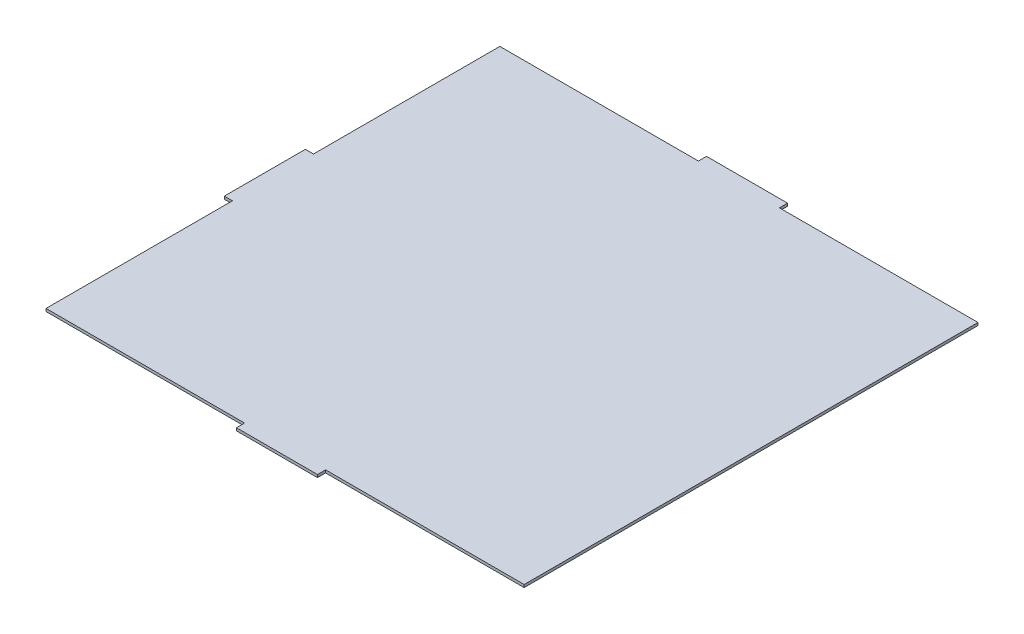
SolidWorks part; units mm, degrees
ref_plane "Front Plane" through (0, 0, 0) normal (0, 0, 1) x (1, 0, 0)
ref_plane "Top Plane" through (0, 0, 0) normal (0, 1, 0) x (1, 0, 0)
ref_plane "Right Plane" through (0, 0, 0) normal (1, 0, 0) x (0, 0, -1)
sketch "Sketch1" plane through (0, 0, 0) normal (0, 1, 0) x (1, 0, 0)
  line L0 (-51.678, 119.992) -> (21.822, 119.992)
  line L1 (21.822, 119.992) -> (21.822, 122.992)
  line L2 (21.822, 122.992) -> (51.822, 122.992)
  line L3 (51.822, 122.992) -> (51.822, 119.992)
  line L4 (51.822, 119.992) -> (125.322, 119.992)
  line L5 (125.322, 119.992) -> (125.322, -48.008)
  line L6 (125.322, -48.008) -> (51.822, -48.008)
  line L7 (51.822, -48.008) -> (51.822, -51.008)
  line L8 (51.822, -51.008) -> (21.822, -51.008)
  line L9 (21.822, -51.008) -> (21.822, -48.008)
  line L10 (21.822, -48.008) -> (-51.678, -48.008)
  line L12 (-54.678, 35.992) -> (125.322, 35.992) construction
  line L13 (36.822, 122.992) -> (36.822, -51.008) construction
  line L15 (-51.678, 50.992) -> (-54.678, 50.992)
  line L16 (-54.678, 50.992) -> (-54.678, 20.992)
  line L17 (-54.678, 20.992) -> (-51.678, 20.992)
  line L18 (-51.678, 119.992) -> (-51.678, 50.992)
  line L19 (-51.678, 20.992) -> (-51.678, -48.008)
  line L32 (36.822, 35.992) -> (53.822, 35.992) construction
  dimension "D1" = 30
  dimension "D2" = 3
  dimension "D3" = 3
  dimension "D4" = 174
  dimension "D5" = 30
  dimension "D6" = 30
  dimension "D7" = 3
  dimension "D8" = 177
  dimension "D9" = 73.5
  dimension "D10" = 73.5
extrude "Boss-Extrude1" add sketch "Sketch1" along normal blind 1
